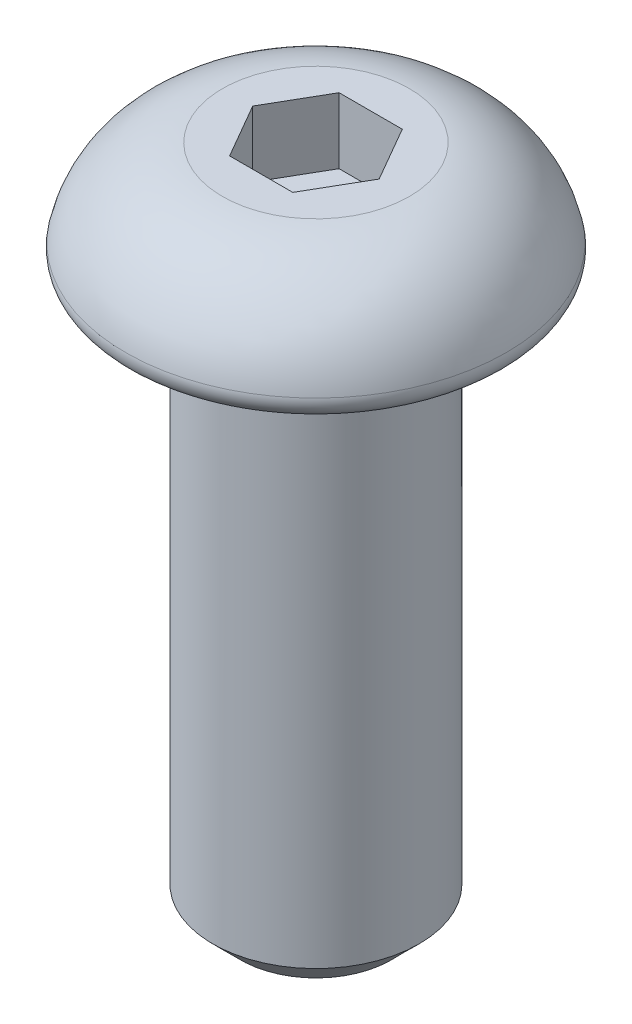
SolidWorks part; units mm, degrees
material "Alloy Steel"
ref_plane "Front Plane" through (0, 0, 0) normal (0, 0, 1) x (1, 0, 0)
ref_plane "Top Plane" through (0, 0, 0) normal (0, 1, 0) x (1, 0, 0)
ref_plane "Right Plane" through (0, 0, 0) normal (1, 0, 0) x (0, 0, -1)
sketch "Sketch1" plane through (0, 0, 0) normal (0, 0, 1) x (1, 0, 0)
  line L0 (1.5875, 1.8542) -> (0, 1.8542)
  line L1 (0, 1.8542) -> (0, 0)
  line L2 (0, 0) -> (3.2706, 0)
  line L3 (0, 1.8542) -> (0, 0) construction
  arc A0 (3.2706, 0) -> (1.5875, 1.8542) centre (1.4077, 0) ccw
revolve "Revolve1" add sketch "Sketch1" angle 360 about L3
sketch "Sketch2" plane through (0, 0, 0) normal (0, -1, 0) x (1, 0, 0)
  circle A0 centre (0, 0) radius 1.7526
extrude "Boss-Extrude1" add sketch "Sketch2" along normal blind 9.525
sketch "Sketch3" plane through (0, 1.8542, 0) normal (0, 1, 0) x (-1, 0, 0)
  line L0 (0.5366, -0.9294) -> (1.0732, 0)
  line L1 (1.0732, 0) -> (0.5366, 0.9294)
  line L2 (0.5366, 0.9294) -> (-0.5366, 0.9294)
  line L3 (-0.5366, 0.9294) -> (-1.0732, 0)
  line L4 (-1.0732, 0) -> (-0.5366, -0.9294)
  line L5 (-0.5366, -0.9294) -> (0.5366, -0.9294)
extrude "Cut-Extrude1" cut sketch "Sketch3" against normal blind 1.1176
chamfer "Chamfer1" distance 0.4724 angle 45 1 edges at (0, -9.525, -1.7526)
fillet "Fillet1" radius 0.3163 2 edges at (0, 0, -1.7526) (3.2706, 0, 0)
